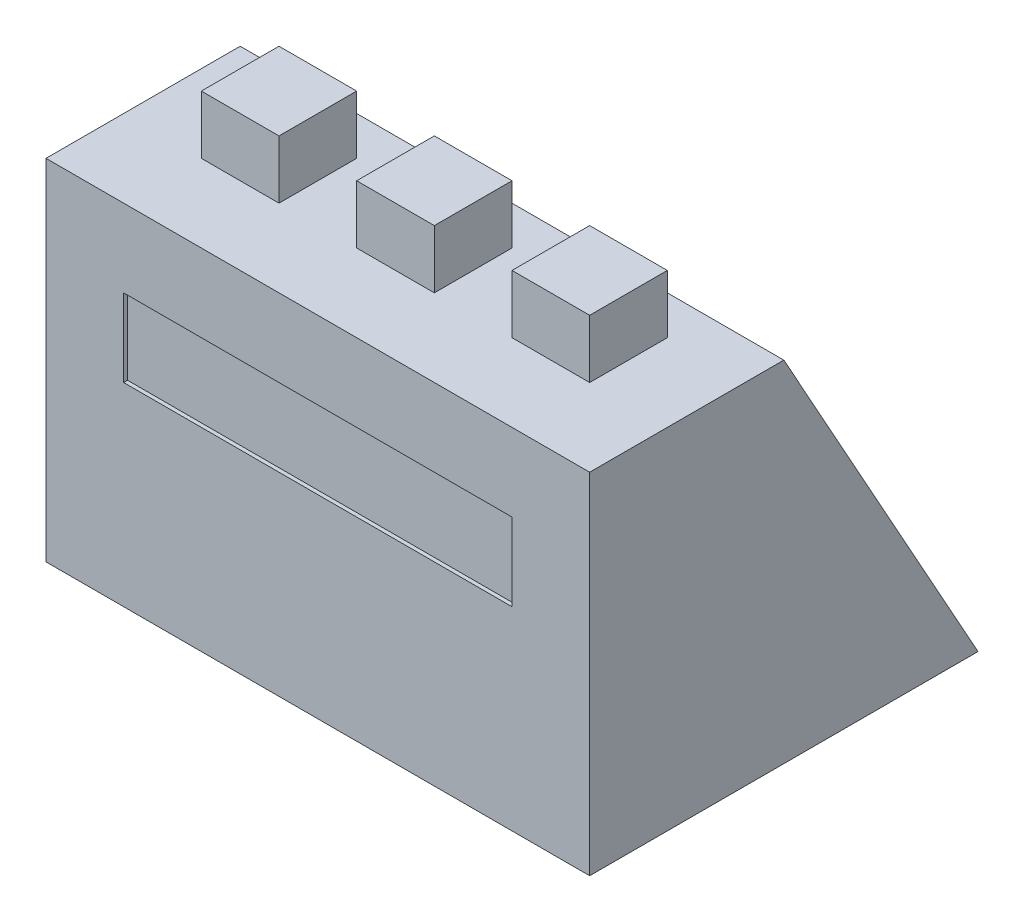
SolidWorks part; units mm, degrees
ref_plane "Front" through (0, 0, 0) normal (0, 0, 1) x (1, 0, 0)
ref_plane "Top" through (0, 0, 0) normal (0, 1, 0) x (1, 0, 0)
ref_plane "Right" through (0, 0, 0) normal (1, 0, 0) x (0, 0, -1)
sketch "Sketch1" plane through (0, 0, 0) normal (1, 0, 0) x (0, 0, -1)
  line L0 (0, 90) -> (0, 0)
  line L1 (0, 0) -> (100, 0)
  line L2 (100, 0) -> (50, 90)
  line L3 (50, 90) -> (0, 90)
  dimension "D1" = 100
  dimension "D2" = 50
  dimension "D3" = 90
extrude "Extrude1" add sketch "Sketch1" along normal blind 140
sketch "Sketch2" plane through (0, 0, 0) normal (0, 0, 1) x (1, 0, 0)
  line L2 (20, 50) -> (120, 50)
  line L3 (20, 70) -> (120, 70)
  line L4 (120, 50) -> (120, 70)
  line L5 (20, 50) -> (20, 70)
  line L6 (0, 50) -> (140, 50) construction
  line L7 (0, 70) -> (140, 70) construction
  line L8 (120, 0) -> (120, 90) construction
  line L9 (20, 0) -> (20, 90) construction
extrude "Cut-Extrude1" cut sketch "Sketch2" against normal blind 1
sketch "Sketch3" plane through (0, 90, 0) normal (0, 1, 0) x (-1, 0, 0)
  line L0 (-140, -50) -> (-140, 0)
  line L1 (-140, 0) -> (0, 0)
  line L2 (-120, -20) -> (-100, -20)
  line L3 (-120, -40) -> (-100, -40)
  line L4 (-120, -40) -> (-120, -20)
  line L5 (-100, -40) -> (-100, -20)
  line L6 (-80, -40) -> (-80, -20)
  line L7 (-140, -20) -> (0, -20) construction
  line L8 (-60, -40) -> (-60, -20)
  line L9 (-40, -40) -> (-40, -20)
  line L10 (-20, -40) -> (-20, -20)
  line L11 (-140, -40) -> (0, -40) construction
  line L12 (-120, -50) -> (-120, 0) construction
  line L13 (-100, -50) -> (-100, 0) construction
  line L14 (-80, -50) -> (-80, 0) construction
  line L15 (-60, -50) -> (-60, 0) construction
  line L16 (-40, -50) -> (-40, 0) construction
  line L17 (-20, -50) -> (-20, 0) construction
  line L18 (-80, -20) -> (-60, -20)
  line L19 (-80, -40) -> (-60, -40)
  line L20 (-40, -20) -> (-20, -20)
  line L21 (-40, -40) -> (-20, -40)
extrude "Extrude2" add sketch "Sketch3" along normal blind 15 separate body contours L21 L10 L20 L9 | L19 L8 L18 L6 | L5 L2 L4 L3
